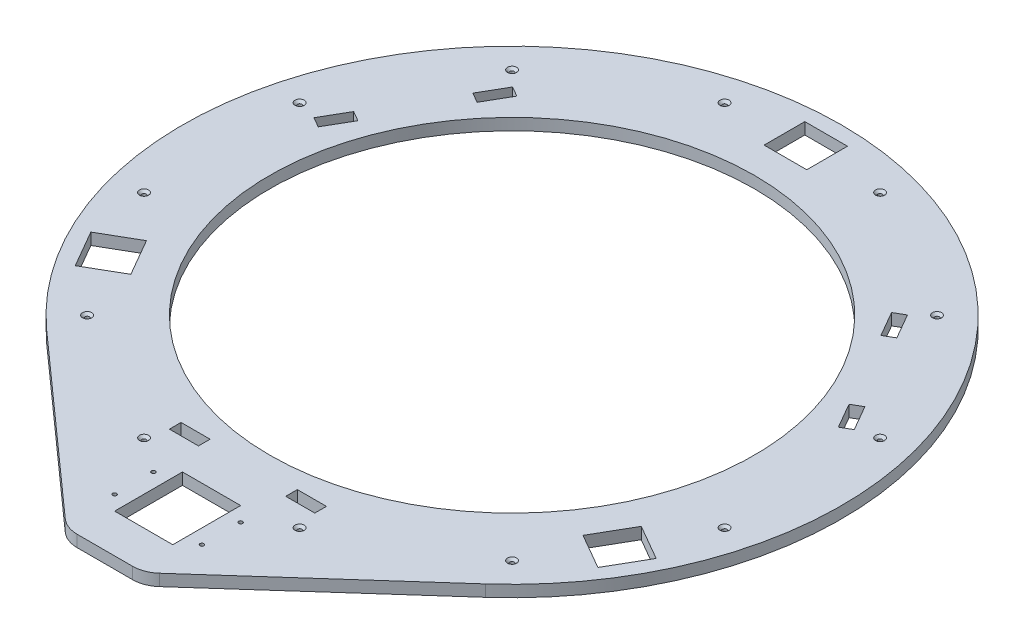
SolidWorks part; units mm, degrees
ref_plane "Front Plane" through (0, 0, 0) normal (0, 0, 1) x (1, 0, 0)
ref_plane "Top Plane" through (0, 0, 0) normal (0, 1, 0) x (1, 0, 0)
ref_plane "Right Plane" through (0, 0, 0) normal (1, 0, 0) x (0, 0, -1)
sketch "Sketch1" plane through (0, 82.4648, 0) normal (0, 1, 0) x (1, 0, 0)
  circle A6 centre (0, 0) radius 340
  circle A12 centre (0, 0) radius 340
  circle A20 centre (0, 0) radius 250
  dimension "D3" = 500
  dimension "D1" = 680
extrude "Boss-Extrude1" add sketch "Sketch1" against normal blind 12
sketch "Sketch7" plane through (0, 70.4648, 0) normal (0, -1, 0) x (1, 0, 0)
  line L0 (75, 278.5) -> (45, 278.5)
  line L1 (75, 266.5) -> (75, 278.5)
  line L2 (45, 266.5) -> (75, 266.5)
  line L3 (45, 278.5) -> (45, 266.5)
  line L4 (-45, 278.5) -> (-45, 266.5)
  line L5 (-45, 266.5) -> (-75, 266.5)
  line L6 (-75, 266.5) -> (-75, 278.5)
  line L7 (-75, 278.5) -> (-45, 278.5)
  line L8 (0, 0) -> (0, 291) construction
  line L9 (-45, 266.5) -> (45, 266.5) construction
  line L10 (-45, 278.5) -> (45, 278.5) construction
  circle A0 centre (0, 0) radius 291 construction
  dimension "D4" = 582
  dimension "D1" = 90
  dimension "D2" = 12
  dimension "D3" = 30
  dimension "D5" = 12.5
extrude "Cut-Extrude2" cut sketch "Sketch7" against normal blind 12
pattern_circular "CirPattern3" count 3 over 360 about axis through (0, 0, 0) along (0, 1, 0) of "Cut-Extrude2"
sketch "Sketch8" plane through (0, 82.4648, 0) normal (0, 1, 0) x (1, 0, 0)
  line L0 (0, 0) -> (0, -420) construction
  line L1 (-40, -420) -> (40, -420)
  line L2 (40, -420) -> (226.3788, -253.6782)
  line L3 (-40, -420) -> (-226.3788, -253.6782)
  circle A1 centre (0, 0) radius 340 construction
  arc A2 (226.3788, -253.6782) -> (-226.3788, -253.6782) centre (0, 0) cw
  dimension "D2" = 80
  dimension "D1" = 420
extrude "Boss-Extrude3" add sketch "Sketch8" against normal blind 12
sketch "Sketch9" plane through (0, 82.4648, 0) normal (0, 1, 0) x (1, 0, 0)
  line L0 (0, 0) -> (0, -380) construction
  line L1 (-30, -380) -> (-30, -310)
  line L2 (-30, -380) -> (30, -380)
  line L4 (-30, -310) -> (30, -310)
  line L5 (30, -380) -> (30, -310)
  dimension "D1" = 60
  dimension "D2" = 70
  dimension "D3" = 310
extrude "Cut-Extrude3" cut sketch "Sketch9" against normal blind 12
sketch "Sketch10" plane through (0, 82.4648, 0) normal (0, 1, 0) x (1, 0, 0)
  line L0 (0, 0) -> (489.6536, -282.7016) construction
  line L1 (0, 0) -> (0, 475.2363) construction
  line L2 (233.2192, -160.0526) -> (255.2192, -121.9474)
  line L5 (255.2192, -121.9474) -> (291.5922, -142.9474)
  line L6 (291.5922, -142.9474) -> (269.5922, -181.0526)
  line L8 (233.2192, -160.0526) -> (269.5922, -181.0526)
  point P14 (255.641, -147.5944)
  point P15 (244.2192, -141)
  dimension "D1" = 120
  dimension "D2" = 282
  dimension "D3" = 44
  dimension "D4" = 42
extrude "Cut-Extrude4" cut sketch "Sketch10" against normal blind 12
pattern_circular "CirPattern4" count 3 over 360 about axis through (0, 0, 0) along (0, 1, 0) of "Cut-Extrude4"
sketch "Sketch11" plane through (0, 82.4648, 0) normal (0, 1, 0) x (1, 0, 0)
  circle A0 centre (-45, -365) radius 2
  circle A1 centre (-45, -325) radius 2
  circle A2 centre (45, -365) radius 2
  circle A3 centre (45, -325) radius 2
  dimension "D1" = 4
extrude "Cut-Extrude5" cut sketch "Sketch11" against normal blind 12
fillet "Fillet1" radius 30 2 edges at (40, 76.4648, 420) (-40, 76.4648, 420)
hole_wizard "CSK for M4 Flat Head Machine Screw" positions "Sketch12" profile "Sketch13" countersink size "M4" standard "ANSI Metric" end condition through all
sketch "Sketch12" plane through (0, 82.4648, 0) normal (0, 1, 0) x (1, 0, 0)
  line L0 (80.2339, 299.437) -> (0, 0) construction
  line L2 (0, 0) -> (0, 423.7069) construction
  circle A0 centre (0, 0) radius 310 construction
  point P0 (80.2339, 299.437)
  point P21 (219.2031, 219.2031)
  point P22 (299.437, 80.2339)
  point P23 (299.437, -80.2339)
  point P24 (219.2031, -219.2031)
  point P25 (80.2339, -299.437)
  point P26 (-80.2339, -299.437)
  point P27 (-219.2031, -219.2031)
  point P28 (-299.437, -80.2339)
  point P29 (-299.437, 80.2339)
  point P30 (-219.2031, 219.2031)
  point P31 (-80.2339, 299.437)
  point P32 (0, 0)
sketch "Sketch13" plane through (80.2339, 82.4648, -299.437) normal (1, 0, 0) x (0, 0, 1)
  line L0 (0, 0) -> (0, 12)
  line L1 (0, 12) -> (2.25, 12)
  line L2 (2.25, 12) -> (2.25, 2.45)
  line L3 (2.25, 2.45) -> (4.7, 0)
  line L4 (4.7, 0) -> (0, 0)
  line L5 (-2.25, 2.45) -> (-4.7, 0) construction
  line L6 (0, -6.35) -> (0, 107.95) construction
  dimension "Thru Hole Dia." = 4.5
  dimension "Thru Hole Depth" = 12
  dimension "Near C'Sink Dia." = 9.4
  dimension "Near C'Sink Angle" = 90
